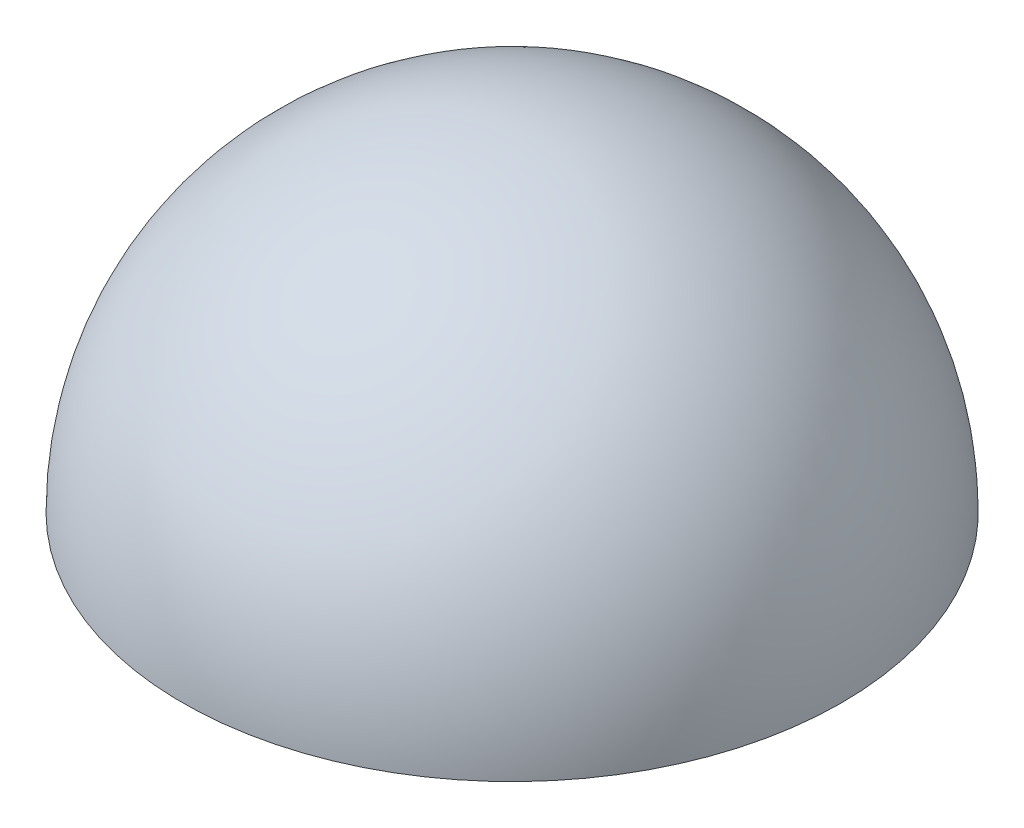
SolidWorks part; units mm, degrees
ref_plane "Front Plane" through (0, 0, 0) normal (0, 0, 1) x (1, 0, 0)
ref_plane "Top Plane" through (0, 0, 0) normal (0, 1, 0) x (1, 0, 0)
ref_plane "Right Plane" through (0, 0, 0) normal (1, 0, 0) x (0, 0, -1)
sketch "Sketch1" plane through (0, 0, 0) normal (0, 1, 0) x (1, 0, 0)
  line L0 (-19.7227, 26.8438) -> (-8.6611, -8.9876)
  circle A0 centre (-14.1919, 8.9281) radius 18.75
  dimension "D1" = 37.5
revolve "Revolve1" add sketch "Sketch1" angle 180 about L0
